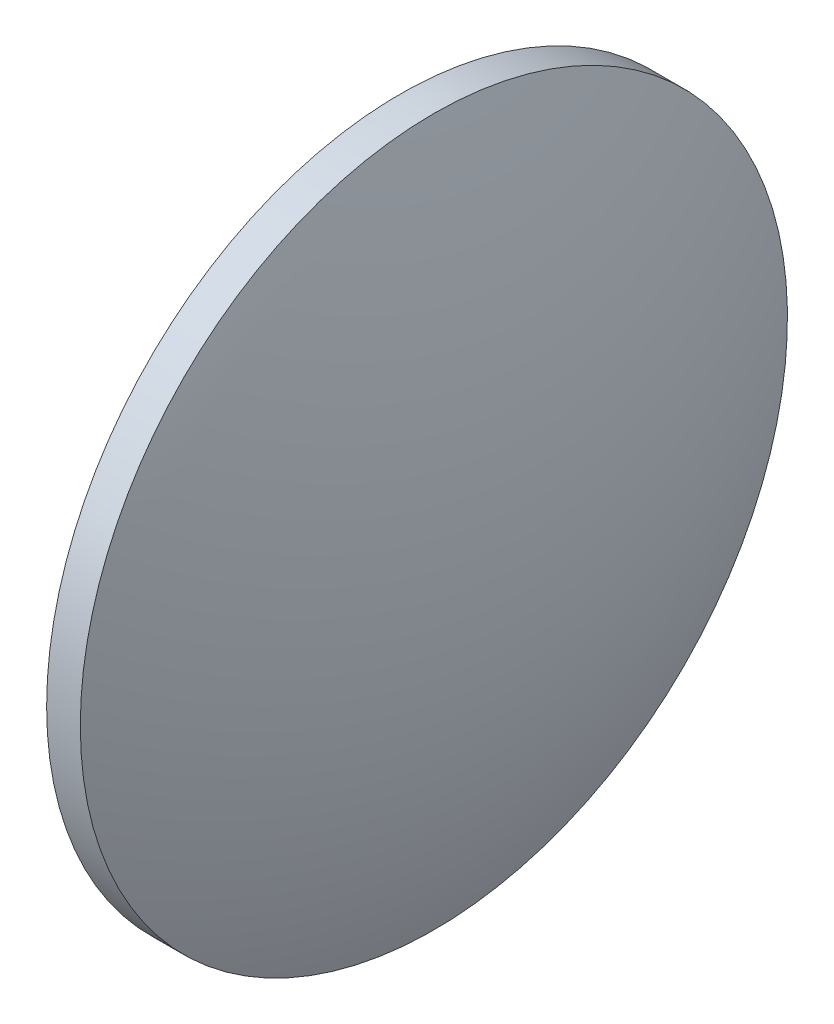
SolidWorks part; units mm, degrees
ref_plane "前视基准面" through (0, 0, 0) normal (0, 0, 1) x (1, 0, 0)
ref_plane "上视基准面" through (0, 0, 0) normal (0, 1, 0) x (1, 0, 0)
ref_plane "右视基准面" through (0, 0, 0) normal (1, 0, 0) x (0, 0, -1)
sketch "草图2" plane through (0, 0, 0) normal (0, 0, 1) x (1, 0, 0)
  line L0 (218.1237, 130.5186) -> (262.0758, 130.5186) construction
  line L1 (226.8933, 130.5186) -> (226.8933, 162.0186)
  line L2 (226.8933, 162.0186) -> (229.8933, 162.0186)
  line L3 (236.1333, 130.5186) -> (226.8933, 130.5186)
  arc A0 (236.1333, 130.5186) -> (229.8933, 162.0186) centre (153.5061, 130.5186) ccw
revolve "旋转1" add sketch "草图2" angle 360 about L0
